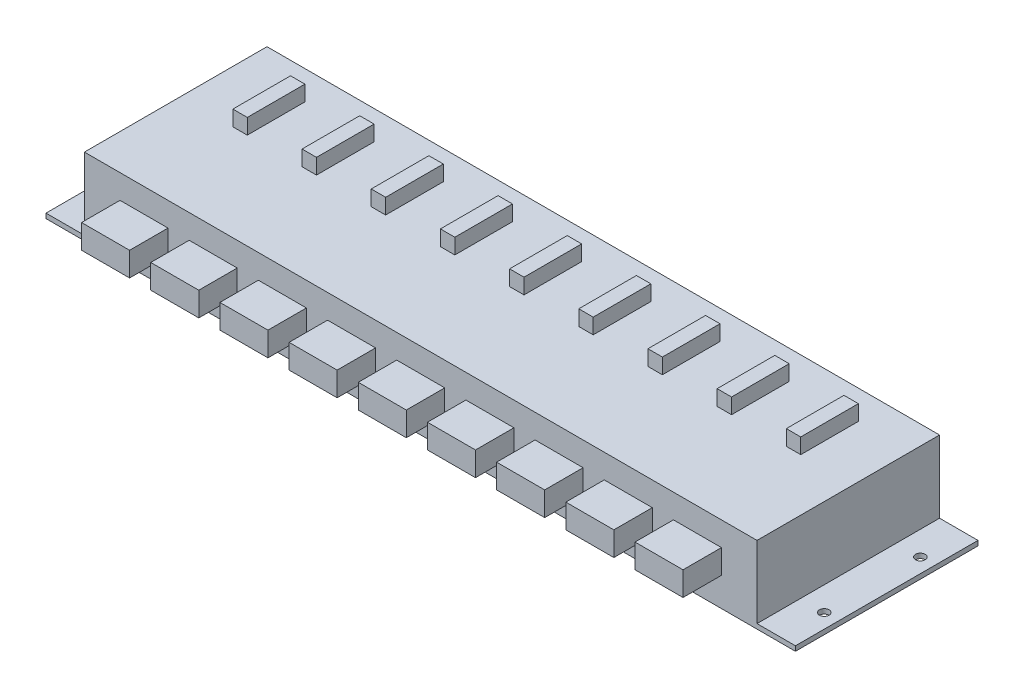
SolidWorks part; units mm, degrees
ref_plane "Front Plane" through (0, 0, 0) normal (0, 0, 1) x (1, 0, 0)
ref_plane "Top Plane" through (0, 0, 0) normal (0, 1, 0) x (1, 0, 0)
ref_plane "Right Plane" through (0, 0, 0) normal (1, 0, 0) x (0, 0, -1)
sketch "Sketch1" plane through (0, 0, 0) normal (0, 1, 0) x (1, 0, 0)
  line L1 (0, 0) -> (222.25, 0)
  line L2 (0, 0) -> (0, 60.325)
  line L3 (0, 60.325) -> (222.25, 60.325)
  line L4 (222.25, 0) -> (222.25, 60.325)
  dimension "D1" = 222.25
  dimension "D2" = 60.325
extrude "Boss-Extrude1" add sketch "Sketch1" along normal blind 25.4
sketch "Sketch2" plane through (0, 0, 0) normal (0, -1, 0) x (1, 0, 0)
  line L0 (222.25, -60.325) -> (0, -60.325) construction
  line L1 (222.25, 0) -> (234.95, 0)
  line L2 (222.25, 0) -> (222.25, -60.325)
  line L3 (222.25, -60.325) -> (234.95, -60.325)
  line L4 (234.95, 0) -> (234.95, -60.325)
  line L5 (0, 0) -> (-12.7, 0)
  line L6 (0, 0) -> (0, -60.325)
  line L7 (0, -60.325) -> (-12.7, -60.325)
  line L8 (-12.7, 0) -> (-12.7, -60.325)
  dimension "D1" = 247.65
extrude "Boss-Extrude2" add sketch "Sketch2" against normal blind 1.5875
sketch "Sketch3" plane through (0, 1.5875, 0) normal (0, 1, 0) x (1, 0, 0)
  line L0 (0, 60.325) -> (222.25, 0) construction
  line L2 (230.1875, 46.0375) -> (-7.9375, 46.0375) construction
  line L3 (230.1875, 46.0375) -> (230.1875, 14.2875) construction
  line L4 (230.1875, 14.2875) -> (-7.9375, 14.2875) construction
  line L5 (-7.9375, 46.0375) -> (-7.9375, 14.2875) construction
  line L6 (230.1875, 46.0375) -> (-7.9375, 14.2875) construction
  line L7 (230.1875, 14.2875) -> (-7.9375, 46.0375) construction
  circle A0 centre (-7.9375, 46.0375) radius 1.5875
  circle A1 centre (-7.9375, 14.2875) radius 1.5875
  circle A2 centre (230.1875, 14.2875) radius 1.5875
  circle A3 centre (230.1875, 46.0375) radius 1.5875
  point P4 (111.125, 30.1625)
  dimension "D1" = 3.175
  dimension "D2" = 238.125
  dimension "D3" = 31.75
extrude "Cut-Extrude1" cut sketch "Sketch3" against normal through all
sketch "Sketch4" plane through (0, 25.4, 0) normal (0, 1, 0) x (1, 0, 0)
  line L0 (111.125, 60.325) -> (111.125, 0) construction
  line L1 (222.25, 60.325) -> (0, 60.325) construction
  line L2 (0, 0) -> (222.25, 0) construction
  line L4 (113.5063, 50.8) -> (108.7438, 50.8)
  line L5 (113.5063, 50.8) -> (113.5063, 31.75)
  line L6 (113.5063, 31.75) -> (108.7438, 31.75)
  line L7 (108.7438, 50.8) -> (108.7438, 31.75)
  line L8 (113.5063, 50.8) -> (108.7438, 31.75) construction
  line L9 (113.5063, 31.75) -> (108.7438, 50.8) construction
  point P6 (111.125, 41.275)
  dimension "D1" = 19.05
  dimension "D2" = 4.7625
  dimension "D3" = 9.525
extrude "Boss-Extrude3" add sketch "Sketch4" along normal blind 5.08
sketch "Sketch5" plane through (0, 0, 0) normal (0, 0, 1) x (1, 0, 0)
  line L0 (111.125, 25.4) -> (111.125, 0) construction
  line L1 (108.7438, 25.4) -> (113.5063, 25.4) construction
  line L2 (-12.7, 0) -> (234.95, 0) construction
  line L4 (119.0625, 17.4625) -> (103.1875, 17.4625)
  line L5 (119.0625, 17.4625) -> (119.0625, 9.525)
  line L6 (119.0625, 9.525) -> (103.1875, 9.525)
  line L7 (103.1875, 17.4625) -> (103.1875, 9.525)
  line L8 (119.0625, 17.4625) -> (103.1875, 9.525) construction
  line L9 (119.0625, 9.525) -> (103.1875, 17.4625) construction
  point P6 (111.125, 13.4938)
  dimension "D1" = 7.9375
  dimension "D2" = 15.875
  dimension "D3" = 9.525
extrude "Boss-Extrude4" add sketch "Sketch5" along normal blind 12.7
pattern_linear "LPattern1" count 5 spacing 22.86 along (1, 0, 0) count 5 spacing 22.86 along (-1, 0, 0) of "Boss-Extrude3", "Boss-Extrude4"
